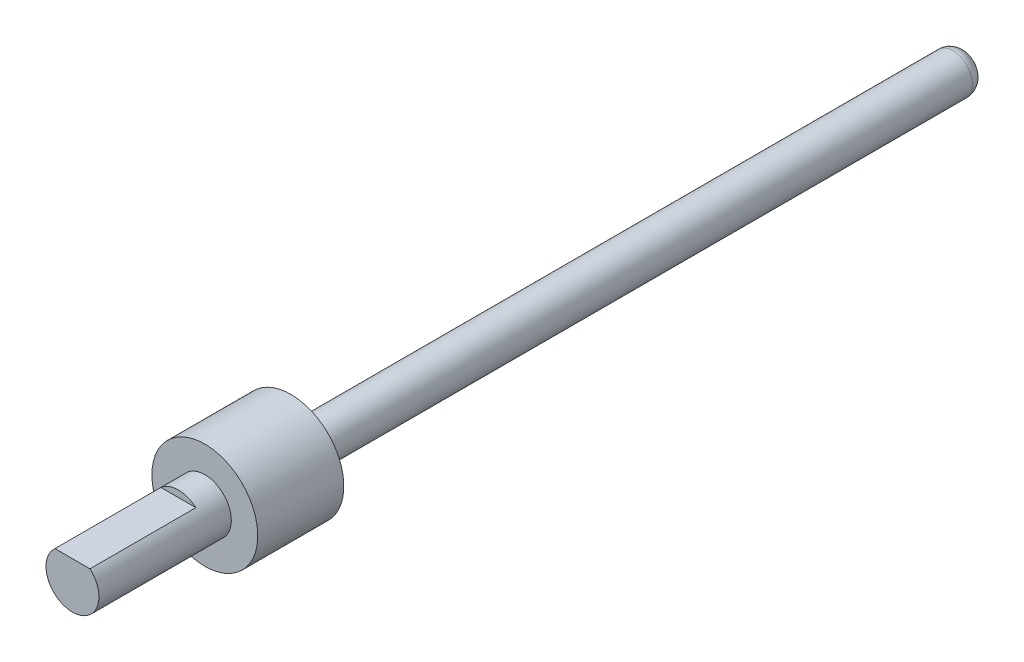
SolidWorks part; units mm, degrees
ref_plane "Front Plane" through (0, 0, 0) normal (0, 0, 1) x (1, 0, 0)
ref_plane "Top Plane" through (0, 0, 0) normal (0, 1, 0) x (1, 0, 0)
ref_plane "Right Plane" through (0, 0, 0) normal (1, 0, 0) x (0, 0, -1)
ref_plane "Plane2" through (0, 0, -33.1) normal (0, 0, 1) x (1, 0, 0)
sketch "Sketch1" plane through (0, 0, 0) normal (0, 0, 1) x (1, 0, 0)
  circle A0 centre (0, 0) radius 2
  dimension "D1" = 4
extrude "Extrude1" add sketch "Sketch1" against normal blind 10
sketch "Sketch2" plane through (0, 0, 0) normal (0, 0, 1) x (1, 0, 0)
  line L0 (-1.3229, 1.5) -> (1.3229, 1.5)
  circle A0 centre (0, 0) radius 2 construction
  arc A1 (1.3229, 1.5) -> (-1.3229, 1.5) centre (0, 0) ccw
  dimension "D1" = 1.5
extrude "Extrude2" cut sketch "Sketch2" against normal blind 8
sketch "Sketch3" plane through (0, 0, -10) normal (0, 0, -1) x (-1, 0, 0)
  circle A0 centre (0, 0) radius 4
  dimension "D1" = 8
extrude "Extrude3" add sketch "Sketch3" along normal blind 6.5
sketch "Sketch19" plane through (0, 0, -16.5) normal (0, 0, -1) x (-1, 0, 0)
  circle A0 centre (0, 0) radius 1.5
  dimension "D1" = 3
extrude "Extrude13" add sketch "Sketch19" along normal blind 51
fillet "Fillet11" radius 1 1 edges at (-1.5, 0, -67.5)
